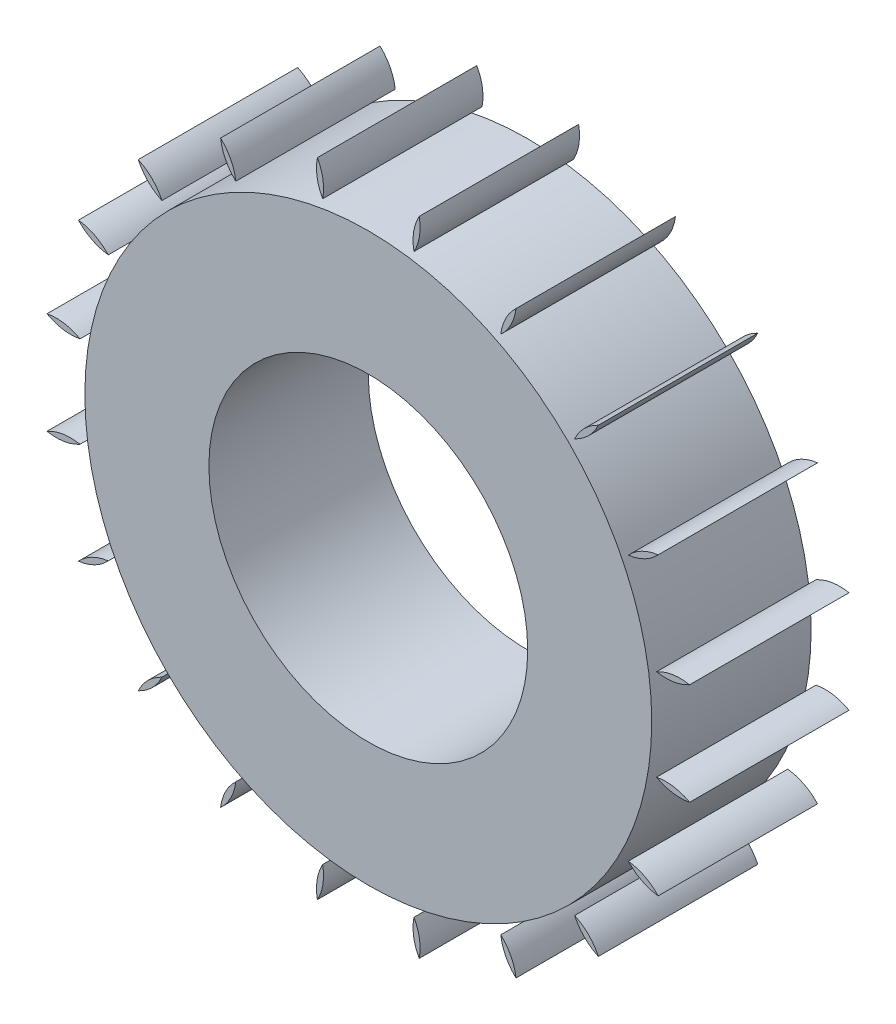
SolidWorks part; units mm, degrees
ref_plane "Front Plane" through (0, 0, 0) normal (0, 0, 1) x (1, 0, 0)
ref_plane "Top Plane" through (0, 0, 0) normal (0, 1, 0) x (1, 0, 0)
ref_plane "Right Plane" through (0, 0, 0) normal (1, 0, 0) x (0, 0, -1)
sketch "Sketch1" plane through (0, 0, 0) normal (0, 0, 1) x (1, 0, 0)
  circle A0 centre (0, 0) radius 6
  circle A1 centre (0, 0) radius 13.2
extrude "Boss-Extrude1" add sketch "Sketch1" along normal blind 6
sketch "Sketch2" plane through (0, 0, 6) normal (0, 0, 1) x (1, 0, 0)
  line L0 (0, 0) -> (0, 15.2) construction
  line L1 (-1.8199, 15.2) -> (0, 0) construction
  line L2 (1.8199, 15.2) -> (0, 0) construction
  arc A0 (-1.8199, 12) -> (1.8199, 12) centre (0, 0) cw
  arc A1 (-2.8199, 12.8953) -> (2.8199, 12.8953) centre (0, 0) cw
  arc A2 (-1.8199, 10.512) -> (1.8199, 10.512) centre (0, 0) cw
  arc A3 (-2.8199, 12.8953) -> (-1.8199, 10.512) centre (-3.5115, 11.2036) cw
  arc A4 (2.8199, 12.8953) -> (1.8199, 10.512) centre (3.5115, 11.2036) ccw
extrude "Cut-Extrude1" cut sketch "Sketch2" against normal through all contours A1 A4 A2 A3
pattern_circular "CirPattern2" count 20 over 360 about axis through (0, 0, 0) along (0, 0, 1) of "Cut-Extrude1"
